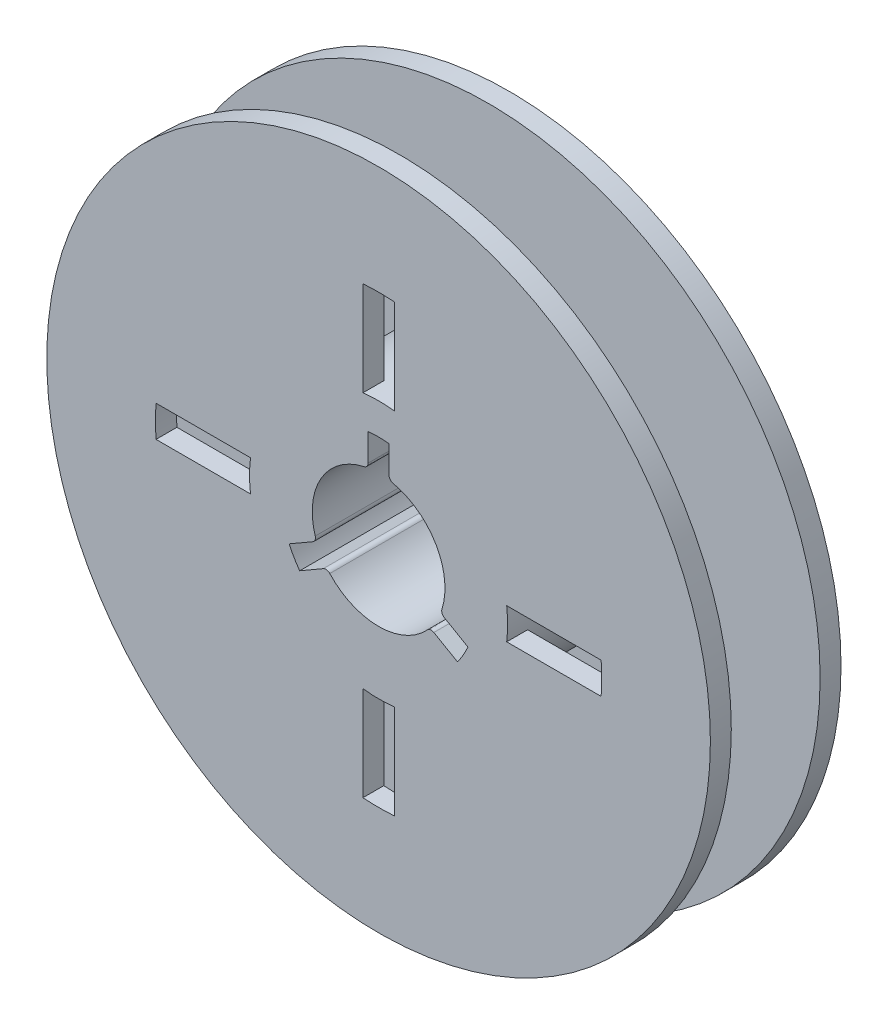
SolidWorks part; units mm, degrees
material "ABS"
ref_plane "Front Plane" through (0, 0, 0) normal (0, 0, 1) x (1, 0, 0)
ref_plane "Top Plane" through (0, 0, 0) normal (0, 1, 0) x (1, 0, 0)
ref_plane "Right Plane" through (0, 0, 0) normal (1, 0, 0) x (0, 0, -1)
sketch "Sketch1" plane through (0, 0, 0) normal (0, 0, 1) x (1, 0, 0)
  line L24 (1.5, 12.2586) -> (1.5, 21.2972)
  line L25 (0, 12.35) -> (0, 21.35) construction
  line L26 (-1.5, 12.2586) -> (-1.5, 21.2972)
  line L27 (-12.2586, 1.5) -> (-21.2972, 1.5)
  line L28 (-12.35, 0) -> (-21.35, 0) construction
  line L29 (-12.2586, -1.5) -> (-21.2972, -1.5)
  line L30 (-1.5, -12.2586) -> (-1.5, -21.2972)
  line L31 (0, -12.35) -> (0, -21.35) construction
  line L32 (1.5, -12.2586) -> (1.5, -21.2972)
  line L33 (12.2586, -1.5) -> (21.2972, -1.5)
  line L34 (12.35, 0) -> (21.35, 0) construction
  line L35 (12.2586, 1.5) -> (21.2972, 1.5)
  circle A1 centre (0, 0) radius 31.75
  arc A2 (-12.2586, 1.5) -> (-12.2586, -1.5) centre (0, 0) ccw
  arc A3 (-21.2972, 1.5) -> (-21.2972, -1.5) centre (0, 0) ccw
  arc A4 (1.5, 21.2972) -> (-1.5, 21.2972) centre (0, 0) ccw
  arc A5 (1.5, 12.2586) -> (-1.5, 12.2586) centre (0, 0) ccw
  arc A6 (12.2586, -1.5) -> (12.2586, 1.5) centre (0, 0) ccw
  arc A7 (21.2972, -1.5) -> (21.2972, 1.5) centre (0, 0) ccw
  arc A8 (-1.5, -21.2972) -> (1.5, -21.2972) centre (0, 0) ccw
  arc A9 (-1.5, -12.2586) -> (1.5, -12.2586) centre (0, 0) ccw
  dimension "D2" = 63.5
  dimension "D4" = 9
extrude "Boss-Extrude1" add sketch "Sketch1" along normal blind 2
sketch "Sketch3" plane through (0, 0, 2) normal (0, 0, 1) x (1, 0, 0)
  circle A0 centre (0, 0) radius 12.35
  dimension "D1" = 24.7
extrude "Boss-Extrude3" add sketch "Sketch3" along normal blind 4.25
mirror "Mirror1" about plane through (0, 0, 6.25) normal (0, 0, 1) of bodies 103
sketch "Sketch4" plane through (0, 0, 0) normal (0, 0, -1) x (-1, 0, 0)
  line L0 (0, 6.35) -> (0, 9.35) construction
  line L2 (5.4993, -3.175) -> (8.0973, -4.675) construction
  line L9 (1, 6.6837) -> (1, 9.2964)
  line L12 (-1, 6.6837) -> (-1, 9.2964)
  line L14 (5.2883, -4.2079) -> (7.5509, -5.5142)
  line L17 (6.2883, -2.4758) -> (8.5509, -3.7822)
  line L19 (-6.2883, -2.4758) -> (-8.5509, -3.7822)
  line L22 (-5.2883, -4.2079) -> (-7.5509, -5.5142)
  line L24 (-5.4993, -3.175) -> (-8.0973, -4.675) construction
  arc A0 (6.061, -1.8937) -> (1.3905, 6.1959) centre (0, 0) ccw
  arc A1 (-8.5509, -3.7822) -> (-7.5509, -5.5142) centre (0, 0) ccw
  arc A2 (1, 9.2964) -> (-1, 9.2964) centre (0, 0) ccw
  arc A3 (7.5509, -5.5142) -> (8.5509, -3.7822) centre (0, 0) ccw
  arc A4 (-4.6705, -4.3022) -> (4.6705, -4.3022) centre (0, 0) ccw
  arc A5 (-1.3905, 6.1959) -> (-6.061, -1.8937) centre (0, 0) ccw
  arc A6 (-4.6705, -4.3022) -> (-5.2883, -4.2079) centre (-5.0383, -4.6409) ccw
  arc A7 (5.2883, -4.2079) -> (4.6705, -4.3022) centre (5.0383, -4.6409) ccw
  arc A8 (6.2883, -2.4758) -> (6.061, -1.8937) centre (6.5383, -2.0428) cw
  arc A9 (1.3905, 6.1959) -> (1, 6.6837) centre (1.5, 6.6837) cw
  arc A10 (-1, 6.6837) -> (-1.3905, 6.1959) centre (-1.5, 6.6837) cw
  arc A11 (-6.061, -1.8937) -> (-6.2883, -2.4758) centre (-6.5383, -2.0428) cw
  point P4 (0, 9.8925)
  point P8 (-4.9306, -4.0014)
  point P9 (8.5672, -4.9462)
  point P46 (-1, 6.2708)
  dimension "D1" = 3
  dimension "D4" = 12.7
  dimension "D5" = 3
  dimension "D6" = 0.5
extrude "Cut-Extrude1" cut sketch "Sketch4" against normal through all
